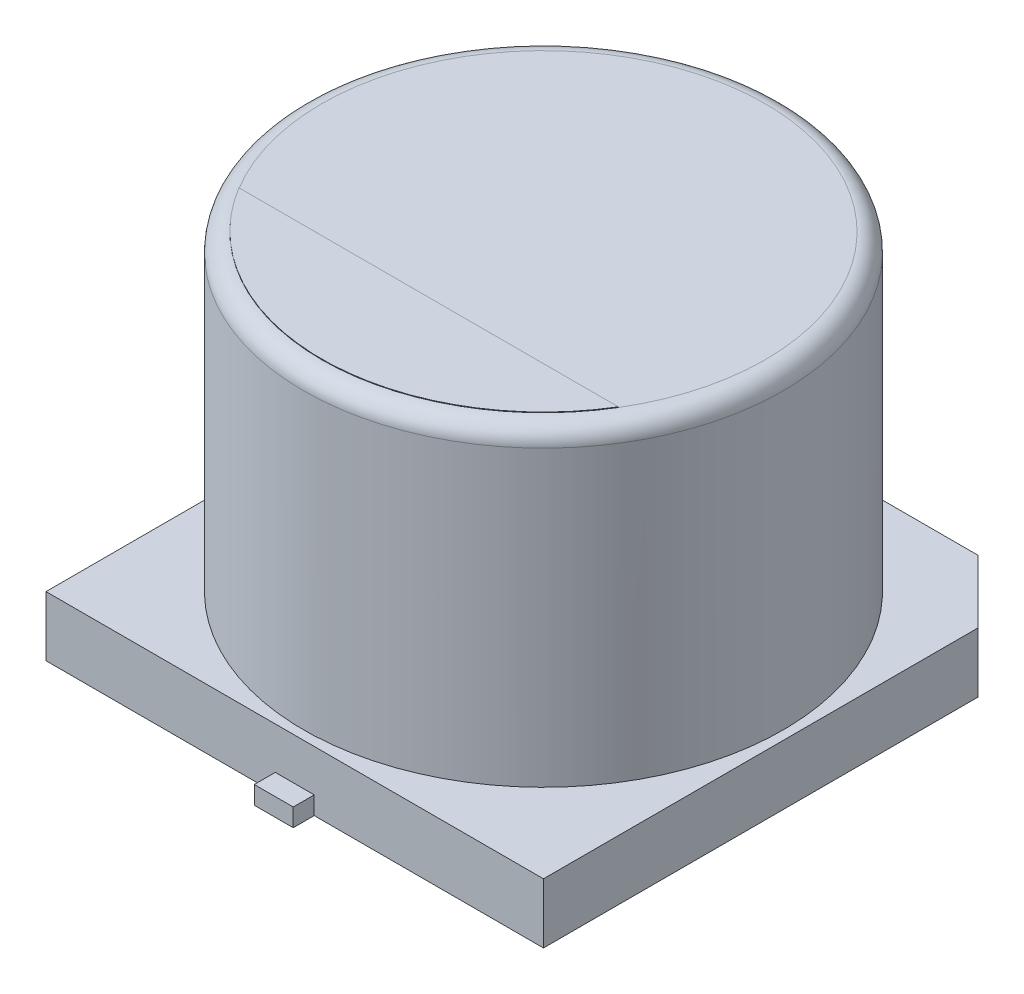
SolidWorks part; units mm, degrees
ref_plane "Front Plane" through (0, 0, 0) normal (0, 0, 1) x (1, 0, 0)
ref_plane "Top Plane" through (0, 0, 0) normal (0, 1, 0) x (1, 0, 0)
ref_plane "Right Plane" through (0, 0, 0) normal (1, 0, 0) x (0, 0, -1)
sketch "Sketch2" plane through (0, 0, 0) normal (0, 1, 0) x (1, 0, 0)
  line L0 (0, 0) -> (0, 2.085) construction
  line L1 (0, 0) -> (2.9643, 0) construction
  line L2 (4.15, -4.15) -> (-4.15, -4.15)
  line L3 (-4.15, -4.15) -> (-4.15, 3.1)
  line L4 (-4.15, 3.1) -> (-3.1, 4.15)
  line L5 (-3.1, 4.15) -> (3.1, 4.15)
  line L6 (3.1, 4.15) -> (4.15, 3.1)
  line L7 (4.15, 3.1) -> (4.15, -4.15)
  line L8 (0, -4.15) -> (0, -0.9795) construction
  line L9 (0, 4.15) -> (0, 2.1922) construction
  line L10 (-0.2934, -4.15) -> (-0.2934, 4.15) construction
  line L11 (-0.2934, 0) -> (-0.8682, 0) construction
  dimension "D1" = 8.3
  dimension "D2" = 8.3
  dimension "D3" = 6.2
extrude "Boss-Extrude1" add sketch "Sketch2" along normal blind 1
sketch "Sketch3" plane through (0, 0, 0) normal (0, 1, 0) x (1, 0, 0)
  circle A0 centre (0, 0) radius 4
  dimension "D1" = 8
extrude "Boss-Extrude2" add sketch "Sketch3" along normal blind 6.2 contours A0
fillet "Fillet1" radius 0.3 1 edges at (0, 6.2, 4)
sketch "Sketch4" plane through (0, 0, 0) normal (0, 1, 0) x (1, 0, 0)
  line L0 (0, 0) -> (7.7959, 0) construction
  line L1 (0.325, 4.5) -> (-0.325, 4.5)
  line L2 (0.325, -1.1) -> (-0.325, -1.1)
  line L3 (0.325, -1.1) -> (0.325, -4.5)
  line L4 (0.325, -4.5) -> (-0.325, -4.5)
  line L5 (-0.325, -1.1) -> (-0.325, -4.5)
  line L6 (0.325, -1.1) -> (-0.325, -4.5) construction
  line L7 (0.325, -4.5) -> (-0.325, -1.1) construction
  line L8 (-0.325, 1.1) -> (-0.325, 4.5)
  line L9 (0.325, 1.1) -> (-0.325, 1.1)
  line L10 (0.325, 1.1) -> (0.325, 4.5)
  line L11 (0.325, 4.5) -> (-0.325, 1.1) construction
  line L12 (0.325, 1.1) -> (-0.325, 4.5) construction
  point P1 (0, -2.8)
  point P12 (0, 2.8)
  dimension "D1" = 0.65
  dimension "D2" = 3.4
  dimension "D3" = 2.2
extrude "Boss-Extrude3" add sketch "Sketch4" along normal blind 0.3
ref_plane "Plane1" through (0, 6.2, 0) normal (0, 1, 0) x (1, 0, 0)
sketch "Sketch5" plane through (0, 6.2, 0) normal (0, 1, 0) x (1, 0, 0)
  line L0 (-3.165, -1.9164) -> (3.165, -1.9164)
  circle A0 centre (0, 0) radius 3.7 construction
  arc A1 (-3.165, -1.9164) -> (3.165, -1.9164) centre (0, 0) ccw
extrude "Boss-Extrude4" add sketch "Sketch5" along normal blind 0.01
